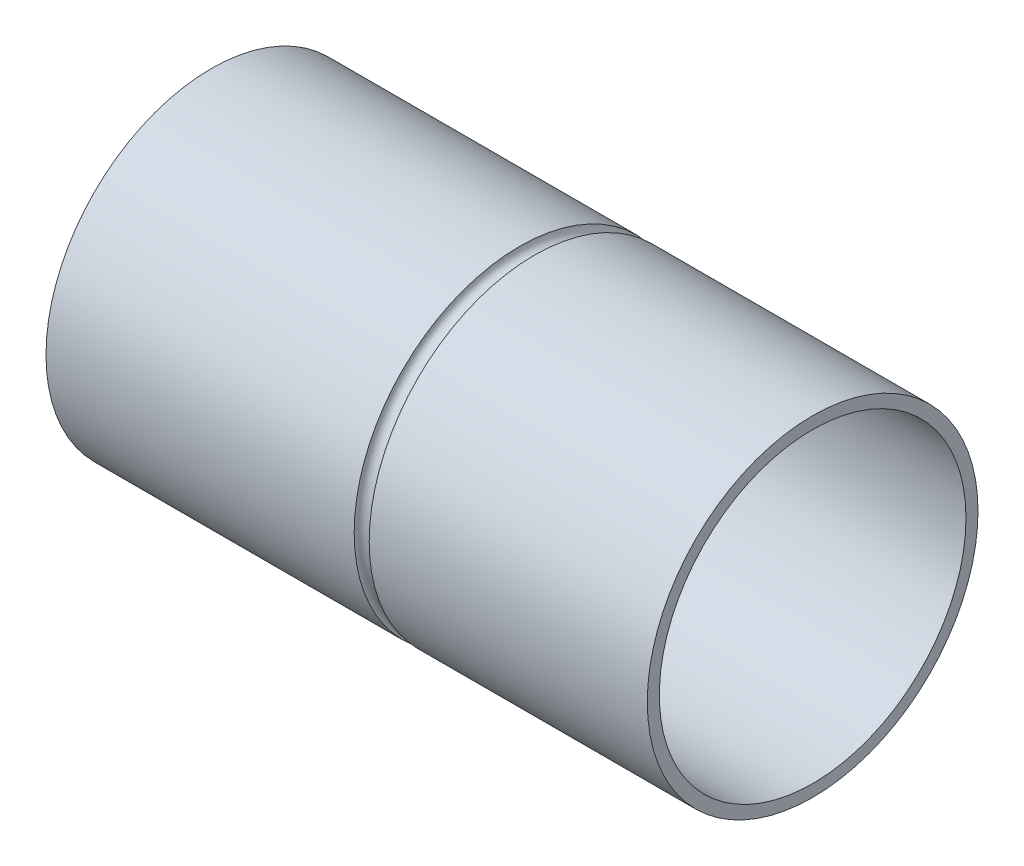
SolidWorks part; units mm, degrees
ref_plane "Front Plane" through (0, 0, 0) normal (0, 0, 1) x (1, 0, 0)
ref_plane "Top Plane" through (0, 0, 0) normal (0, 1, 0) x (1, 0, 0)
ref_plane "Right Plane" through (0, 0, 0) normal (1, 0, 0) x (0, 0, -1)
sketch "Sketch1" plane through (0, 0, 0) normal (1, 0, 0) x (0, 0, -1)
  circle A0 centre (0, 0) radius 55
extrude "Boss-Extrude1" add sketch "Sketch1" along normal blind 200
sketch "Sketch2" plane through (200, 0, 0) normal (1, 0, 0) x (0, 0, -1)
  circle A0 centre (0, 0) radius 51
extrude "Cut-Extrude1" cut sketch "Sketch2" against normal blind 190
sketch "Sketch3" plane through (0, 0, 0) normal (-1, 0, 0) x (0, 0, 1)
  circle A0 centre (0, 0) radius 19
extrude "Cut-Extrude2" cut sketch "Sketch3" against normal through all both and the other way through all
sketch "Sketch4" plane through (0, 0, 0) normal (-1, 0, 0) x (0, 0, 1)
  circle A0 centre (0, 34) radius 5
  circle A1 centre (0, -34) radius 5
extrude "Cut-Extrude3" cut sketch "Sketch4" against normal blind 2
sketch "Sketch5" plane through (0, 0, 0) normal (-1, 0, 0) x (0, 0, 1)
  circle A0 centre (0, 0) radius 22.5
extrude "Cut-Extrude4" cut sketch "Sketch5" against normal blind 2
sketch "Sketch13" plane through (0, 0, 0) normal (0, 1, 0) x (1, 0, 0)
  line L0 (-100, 0) -> (100, 0) construction
  point P4 (0, 0)
sketch3d "3DSketch5" plane through (0, 0, 0) normal (0, 0, 1) x (1, 0, 0)
  dimension "D1" = 105
sketch "Sketch57" plane through (105, 0, 0) normal (1, 0, 0) x (0, 0, -1)
  circle A0 centre (0, 0) radius 55
sweep "Cut-Sweep1" cut path "Sketch57" circular profile diameter 5 parameters "D3"=5
sketch "Sketch58" plane through (2, 0, 0) normal (-1, 0, 0) x (0, 0, 1)
  circle A0 centre (0, 34) radius 2.5
  circle A1 centre (0, -34) radius 2.5
extrude "Cut-Extrude5" cut sketch "Sketch58" against normal blind 2
